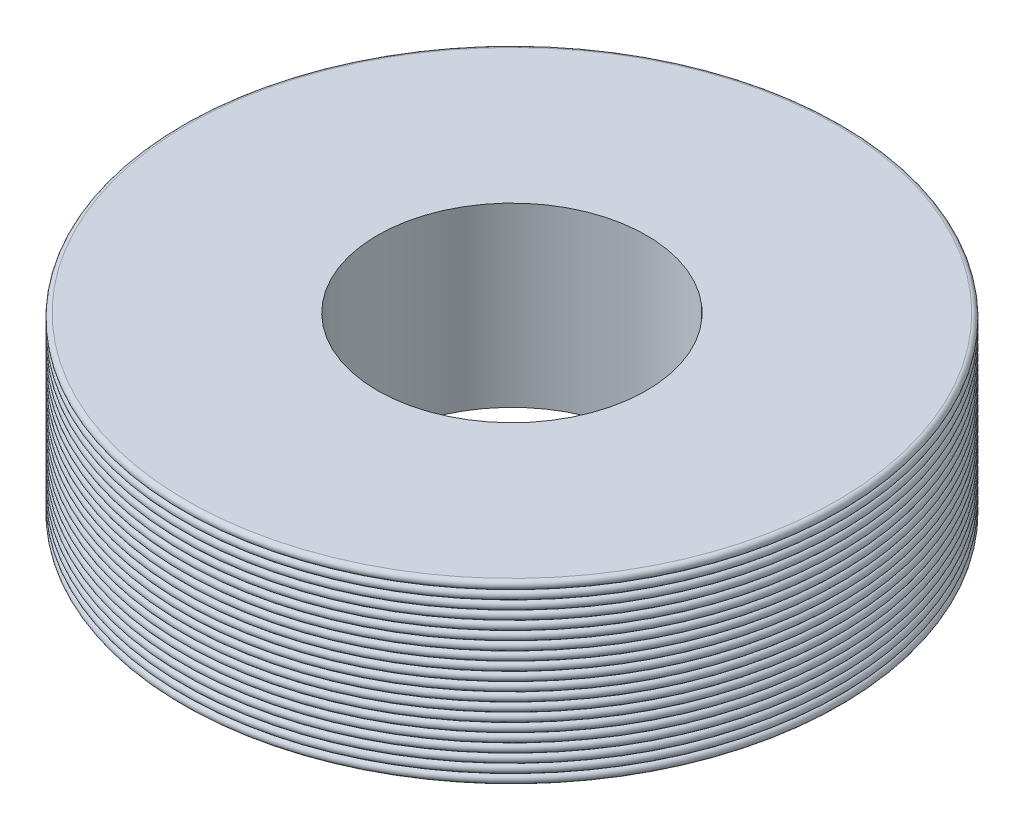
SolidWorks part; units mm, degrees
ref_plane "Front Plane" through (0, 0, 0) normal (0, 0, 1) x (1, 0, 0)
ref_plane "Top Plane" through (0, 0, 0) normal (0, 1, 0) x (1, 0, 0)
ref_plane "Right Plane" through (0, 0, 0) normal (1, 0, 0) x (0, 0, -1)
sketch "Sketch1" plane through (0, 0, 0) normal (0, 1, 0) x (1, 0, 0)
  circle A0 centre (0, 0) radius 40
  circle A1 centre (0, 0) radius 98
  dimension "D1" = 80
  dimension "D2" = 196
extrude "Boss-Extrude1" add sketch "Sketch1" along normal blind 52.6
sketch "Sketch2" plane through (0, 0, 0) normal (0, 0, 1) x (1, 0, 0)
  line L1 (-101.5479, 52.6) -> (-101.5479, 0)
  line L2 (98, 52.6) -> (-98, 52.6) construction
  line L3 (-96.685, 52.6) -> (-101.5479, 52.6)
  line L4 (-98, 0) -> (98, 0) construction
  line L5 (-101.5479, 0) -> (-96.685, 0)
  line L6 (0, 0) -> (0, 57.0027) construction
  arc A0 (-96.685, 52.6) -> (-96.685, 49.97) centre (-96.685, 51.285) ccw
  arc A1 (-96.685, 49.97) -> (-96.685, 47.34) centre (-96.685, 48.655) ccw
  arc A2 (-96.685, 47.34) -> (-96.685, 44.71) centre (-96.685, 46.025) ccw
  arc A3 (-96.685, 44.71) -> (-96.685, 42.08) centre (-96.685, 43.395) ccw
  arc A4 (-96.685, 42.08) -> (-96.685, 39.45) centre (-96.685, 40.765) ccw
  arc A5 (-96.685, 39.45) -> (-96.685, 36.82) centre (-96.685, 38.135) ccw
  arc A6 (-96.685, 36.82) -> (-96.685, 34.19) centre (-96.685, 35.505) ccw
  arc A7 (-96.685, 34.19) -> (-96.685, 31.56) centre (-96.685, 32.875) ccw
  arc A8 (-96.685, 31.56) -> (-96.685, 28.93) centre (-96.685, 30.245) ccw
  arc A9 (-96.685, 28.93) -> (-96.685, 26.3) centre (-96.685, 27.615) ccw
  arc A10 (-96.685, 26.3) -> (-96.685, 23.67) centre (-96.685, 24.985) ccw
  arc A11 (-96.685, 23.67) -> (-96.685, 21.04) centre (-96.685, 22.355) ccw
  arc A12 (-96.685, 21.04) -> (-96.685, 18.41) centre (-96.685, 19.725) ccw
  arc A13 (-96.685, 18.41) -> (-96.685, 15.78) centre (-96.685, 17.095) ccw
  arc A14 (-96.685, 15.78) -> (-96.685, 13.15) centre (-96.685, 14.465) ccw
  arc A15 (-96.685, 13.15) -> (-96.685, 10.52) centre (-96.685, 11.835) ccw
  arc A16 (-96.685, 10.52) -> (-96.685, 7.89) centre (-96.685, 9.205) ccw
  arc A17 (-96.685, 7.89) -> (-96.685, 5.26) centre (-96.685, 6.575) ccw
  arc A18 (-96.685, 5.26) -> (-96.685, 2.63) centre (-96.685, 3.945) ccw
  arc A19 (-96.685, 2.63) -> (-96.685, 0) centre (-96.685, 1.315) ccw
  dimension "D1" = 2.63
  dimension "D2" = 20
revolve "Cut-Revolve1" cut sketch "Sketch2" angle 360 about L6
